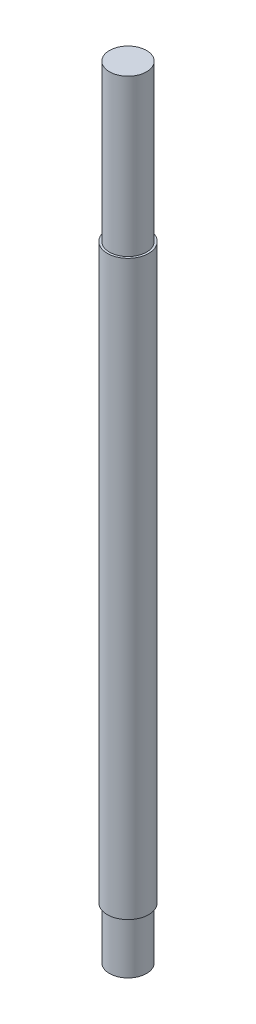
SolidWorks part; units mm, degrees
material "6061-T4 (SS)"
ref_plane "Front Plane" through (0, 0, 0) normal (0, 0, 1) x (1, 0, 0)
ref_plane "Top Plane" through (0, 0, 0) normal (0, 1, 0) x (1, 0, 0)
ref_plane "Right Plane" through (0, 0, 0) normal (1, 0, 0) x (0, 0, -1)
sketch "Sketch1" plane through (0, 0, 0) normal (0, 1, 0) x (1, 0, 0)
  circle A0 centre (0, 0) radius 1.5875
  dimension "D1" = 3.175
extrude "Boss-Extrude1" add sketch "Sketch1" along normal blind 60 contours A0
sketch "Sketch2" plane through (0, 0, 0) normal (0, -1, 0) x (1, 0, 0)
  line L0 (0, 1.4224) -> (0, 1.5875) construction
  circle A0 centre (0, 0) radius 1.5875
  circle A1 centre (0, 0) radius 1.4224
  circle A2 centre (0, 0) radius 1.5875 construction
  dimension "D1" = 2.8448
extrude "Cut-Extrude1" cut sketch "Sketch2" against normal blind 4
chamfer "Chamfer1" [suppressed] distance 0.2 angle 45
thread "Thread1" [suppressed] pitch 0.635 start angle 0, offset 0, length 0, pitch 0.635, diameter 2.8448
ref_plane "Plane2" through (-1.4224, 4, 0) normal (0, 0, 1) x (-1, 0, 0)
sketch "Thread Profile2" plane through (-1.4224, 4, 0) normal (0, 0, 1) x (-1, 0, 0)
  line L0 (0, 0) -> (0, 0.635) construction
  line L11 (0, 0) -> (0, 0.5556)
  line L12 (0, 0.5556) -> (-0.3437, 0.3572)
  line L13 (-0.3437, 0.3572) -> (-0.3437, 0.1984)
  line L15 (-0.3437, 0.1984) -> (0, 0)
  line L17 (-0.3437, 0.2778) -> (0, 0.2778) construction
  point P2 (0, 0)
  dimension "Pitch" = 0.635
  dimension "Profile_Angle" = 60
  dimension "Profile_Land" = 0.1588
  dimension "Profile_Height" = 0.3437
sketch "Sketch7" plane through (0, 60, 0) normal (0, 1, 0) x (1, 0, 0)
  circle A0 centre (0, 0) radius 1.5875
  circle A1 centre (0, 0) radius 1.4224
  circle A2 centre (0, 0) radius 1.5875 construction
  dimension "D1" = 2.8448
extrude "Cut-Extrude2" cut sketch "Sketch7" against normal blind 12
chamfer "Chamfer2" [suppressed] distance 0.2 angle 45
thread "Thread2" [suppressed] pitch 0.635 start angle 0, offset 0, length 0, pitch 0.635, diameter 2.8448
ref_plane "Plane3" through (1.4224, 50, 0) normal (0, 0, 1) x (1, 0, 0)
sketch "Thread Profile3" plane through (1.4224, 50, 0) normal (0, 0, 1) x (1, 0, 0)
  line L0 (0, 0) -> (0, 0.635) construction
  line L11 (0, 0) -> (0, 0.5556)
  line L12 (0, 0.5556) -> (-0.3437, 0.3572)
  line L13 (-0.3437, 0.3572) -> (-0.3437, 0.1984)
  line L15 (-0.3437, 0.1984) -> (0, 0)
  line L17 (-0.3437, 0.2778) -> (0, 0.2778) construction
  point P2 (0, 0)
  dimension "Pitch" = 0.635
  dimension "Profile_Angle" = 60
  dimension "Profile_Land" = 0.1588
  dimension "Profile_Height" = 0.3437
